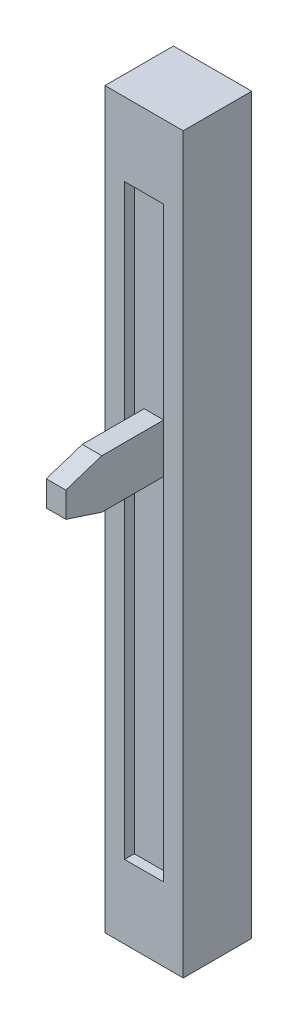
SolidWorks part; units mm, degrees
ref_plane "Front Plane" through (0, 0, 0) normal (0, 0, 1) x (1, 0, 0)
ref_plane "Top Plane" through (0, 0, 0) normal (0, 1, 0) x (1, 0, 0)
ref_plane "Right Plane" through (0, 0, 0) normal (1, 0, 0) x (0, 0, -1)
sketch "Sketch1" plane through (0, 0, 0) normal (0, 0, 1) x (1, 0, 0)
  line L1 (-4, -37.5) -> (4, -37.5)
  line L2 (-4, -37.5) -> (-4, 37.5)
  line L3 (-4, 37.5) -> (4, 37.5)
  line L4 (4, -37.5) -> (4, 37.5)
  line L5 (-4, -37.5) -> (4, 37.5) construction
  line L6 (-4, 37.5) -> (4, -37.5) construction
  point P0 (0, 0)
  dimension "D1" = 75
  dimension "D2" = 8
extrude "Boss-Extrude1" add sketch "Sketch1" along normal blind 7
sketch "Sketch2" plane through (0, 0, 7) normal (0, 0, 1) x (1, 0, 0)
  line L1 (-2, -30) -> (2, -30)
  line L2 (-2, -30) -> (-2, 30)
  line L3 (-2, 30) -> (2, 30)
  line L4 (2, -30) -> (2, 30)
  line L5 (-2, -30) -> (2, 30) construction
  line L6 (-2, 30) -> (2, -30) construction
  point P0 (0, 0)
  dimension "D1" = 60
  dimension "D2" = 4
extrude "Cut-Extrude1" cut sketch "Sketch2" against normal blind 1
sketch "Sketch3" plane through (0, 0, 0) normal (1, 0, 0) x (0, 0, -1)
  line L0 (-5.3629, 9.8951) -> (-12.3256, 9.8951)
  line L1 (-12.3256, 9.8951) -> (-16, 8.6893)
  line L2 (-16, 8.6893) -> (-16, 6.101)
  line L3 (-16, 6.101) -> (-12.3256, 4.8951)
  line L4 (-12.3256, 4.8951) -> (-5.3629, 4.8951)
  line L5 (-5.3629, 4.8951) -> (-5.3629, 9.8951)
  line L6 (-7, -37.5) -> (-7, 37.5) construction
  line L7 (-16, 7.3951) -> (-5.3629, 7.3951) construction
  dimension "D1" = 9
  dimension "D2" = 5
extrude "Boss-Extrude2" add sketch "Sketch3" along normal mid plane 2
